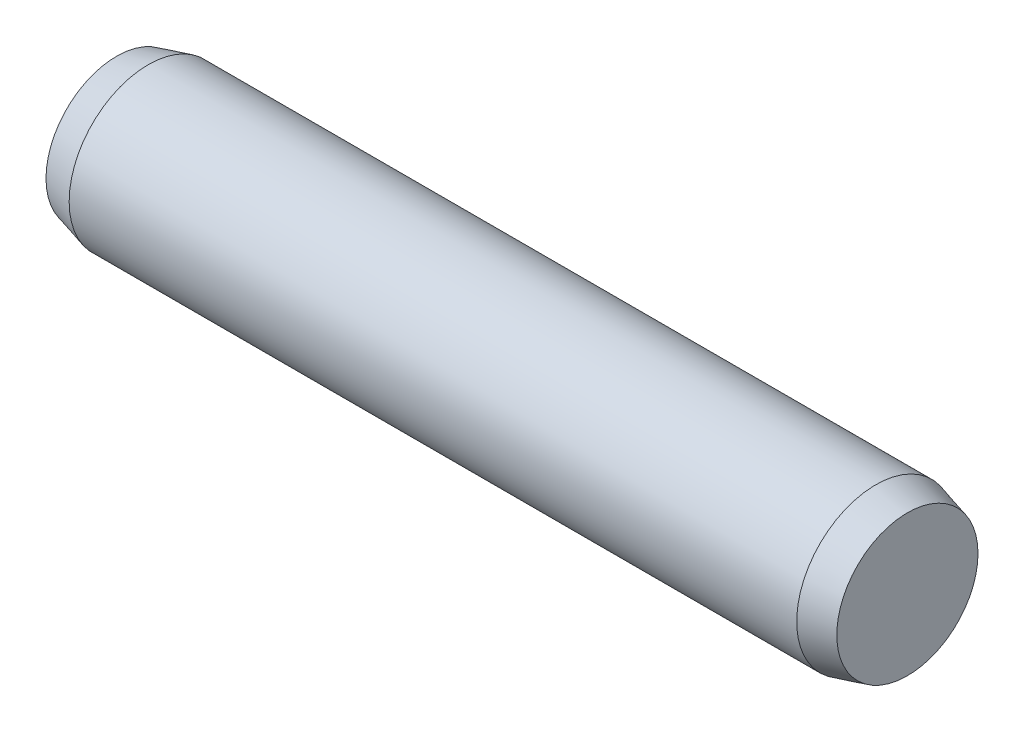
SolidWorks part; units mm, degrees
ref_plane "Front Plane" through (0, 0, 0) normal (0, 0, 1) x (1, 0, 0)
ref_plane "Top Plane" through (0, 0, 0) normal (0, 1, 0) x (1, 0, 0)
ref_plane "Right Plane" through (0, 0, 0) normal (1, 0, 0) x (0, 0, -1)
sketch "Sketch1" plane through (0, 0, 0) normal (0, 0, 1) x (1, 0, 0)
  line L0 (-13.8, 0) -> (13.8, 0) construction
  line L1 (13.8, 3) -> (13.8, -3) construction
  line L2 (-13.8, 3) -> (-13.8, -3) construction
  line L3 (15, 3) -> (15, -3) construction
  line L4 (-15, 3) -> (-15, -3) construction
  line L5 (-13.8, 0) -> (-15, 0) construction
  line L6 (13.8, 0) -> (15, 0) construction
  point P11 (9, 0)
  point P21 (-9, 0)
  dimension "Dia" = 6
  dimension "C" = 1.2
  dimension "D1" = 1.2
  dimension "Length" = 30
  dimension "D2" = 6
  dimension "D3" = 6
sketch "Sketch2" plane through (0, 0, 0) normal (1, 0, 0) x (0, 0, -1)
  circle A0 centre (0, 0) radius 3
extrude "Extrude1" add sketch "Sketch2" against normal up to vertex (13.8 mm away) and the other way up to vertex (13.8 mm away) up to point (-13.8, 3, 0) other way up to point (13.8, 3, 0)
sketch "Sketch3" plane through (13.8, 0, 0) normal (1, 0, 0) x (0, 0, -1)
  circle A1 centre (0, 0) radius 3
  circle A2 centre (0, 0) radius 3
  dimension "D1" = 0
extrude "Extrude2" add sketch "Sketch3" along normal up to vertex (1.2 mm away) draft 15 up to point (15, 0, 0)
sketch "Sketch4" plane through (-13.8, 0, 0) normal (-1, 0, 0) x (0, 0, 1)
  circle A1 centre (0, 0) radius 3
  circle A2 centre (0, 0) radius 3
  dimension "D1" = 0
extrude "Extrude3" add sketch "Sketch4" along normal up to vertex (1.2 mm away) draft 15 up to point (-15, 0, 0)
sketch "Sketch5" plane through (0, 0, 0) normal (1, 0, 0) x (0, 0, -1)
  line L0 (-3, 0) -> (3, 0) construction
  point P4 (0, 0)
  dimension "D1" = 6
equation "\"D1@Sketch1\" = \"C@Sketch1\""
equation "\"D1@Sketch5\" = \"Dia@Sketch1\""
equation "\"D2@Sketch1\"=\"Dia@Sketch1\""
equation "\"D3@Sketch1\"=\"D2@Sketch1\""
